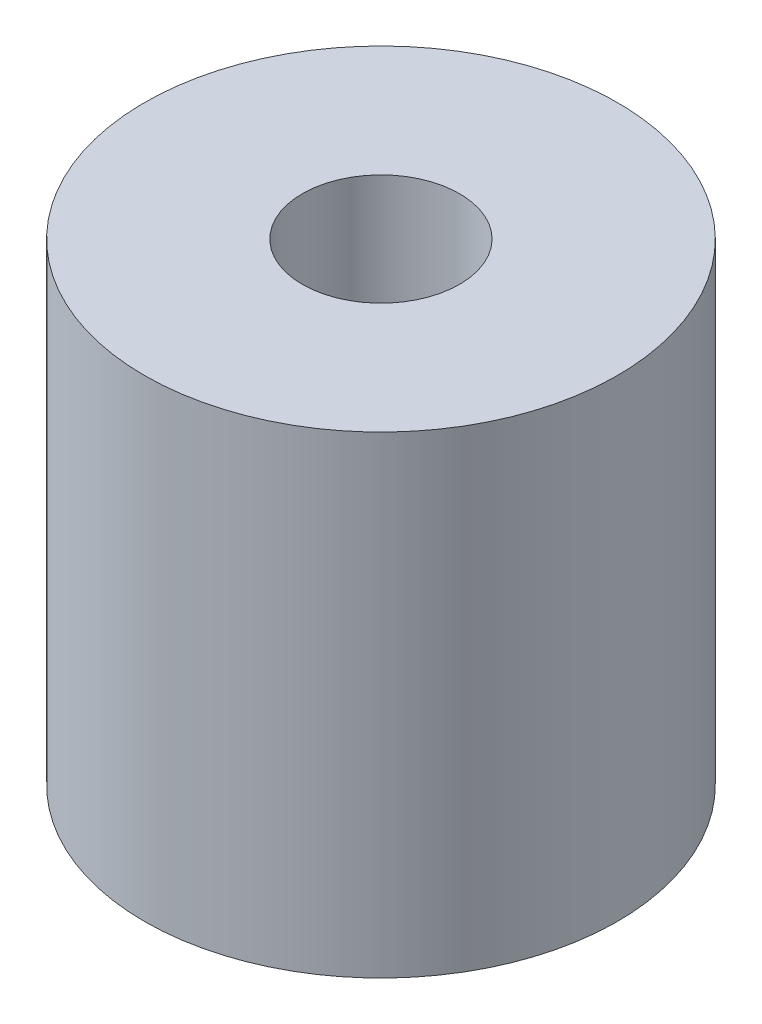
SolidWorks part; units mm, degrees
ref_plane "Front Plane" through (0, 0, 0) normal (0, 0, 1) x (1, 0, 0)
ref_plane "Top Plane" through (0, 0, 0) normal (0, 1, 0) x (1, 0, 0)
ref_plane "Right Plane" through (0, 0, 0) normal (1, 0, 0) x (0, 0, -1)
sketch "Sketch1" plane through (0, 0, 0) normal (0, 1, 0) x (1, 0, 0)
  circle A0 centre (0, 0) radius 12.7
  circle A1 centre (0, 0) radius 4.2227
  dimension "D1" = 8.4455
  dimension "D2" = 25.4
extrude "Boss-Extrude1" add sketch "Sketch1" along normal blind 25.4
